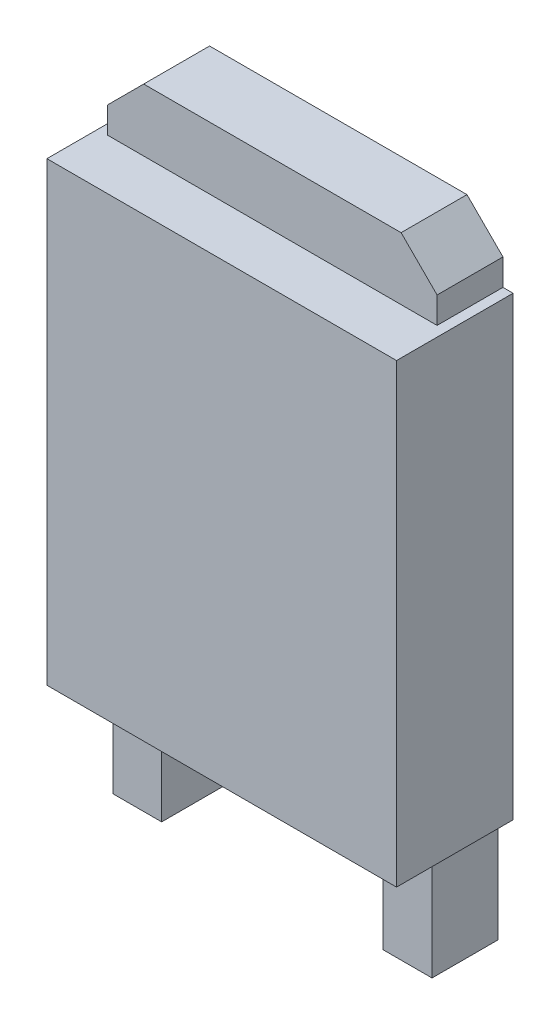
SolidWorks part; units mm, degrees
ref_plane "Front Plane" through (0, 0, 0) normal (0, 0, 1) x (1, 0, 0)
ref_plane "Top Plane" through (0, 0, 0) normal (0, 1, 0) x (1, 0, 0)
ref_plane "Right Plane" through (0, 0, 0) normal (1, 0, 0) x (0, 0, -1)
sketch "Sketch1" plane through (0, 0, 0) normal (0, 0, 1) x (1, 0, 0)
  line L1 (-3.45, -4.5) -> (3.45, -4.5)
  line L2 (-3.45, -4.5) -> (-3.45, 4.5)
  line L3 (-3.45, 4.5) -> (3.45, 4.5)
  line L4 (3.45, -4.5) -> (3.45, 4.5)
  line L5 (-3.45, -4.5) -> (3.45, 4.5) construction
  line L6 (-3.45, 4.5) -> (3.45, -4.5) construction
  point P0 (0, 0)
  dimension "D1" = 6.9
  dimension "D2" = 9
extrude "Boss-Extrude1" add sketch "Sketch1" along normal blind 2.3
sketch "Sketch2" plane through (0, 0, 0) normal (0, 0, -1) x (-1, 0, 0)
  line L0 (3.25, 4.5) -> (3.25, 5.0204)
  line L1 (-3.45, 4.5) -> (3.45, 4.5) construction
  line L2 (2.54, 5.7304) -> (-2.54, 5.7304)
  line L3 (-3.25, 5.0204) -> (-3.25, 4.5)
  line L4 (-3.25, 4.5) -> (3.25, 4.5)
  line L5 (-2.54, 5.7304) -> (-3.25, 5.0204)
  line L6 (3.25, 5.0204) -> (2.54, 5.7304)
  line L7 (-3.15, -4.5) -> (-3.15, -6.7031)
  line L8 (3.45, -4.5) -> (-3.45, -4.5) construction
  line L9 (-3.15, -6.7031) -> (-2.1853, -6.7031)
  line L10 (-2.1853, -6.7031) -> (-2.1853, -4.5)
  line L11 (-3.15, -4.5) -> (-2.1853, -4.5)
  line L12 (0, 0) -> (0, -2.7944) construction
  line L13 (3.15, -4.5) -> (3.15, -6.7031)
  line L14 (3.15, -6.7031) -> (2.1853, -6.7031)
  line L15 (2.1853, -6.7031) -> (2.1853, -4.5)
  line L16 (3.15, -4.5) -> (2.1853, -4.5)
  point P1 (3.25, 5.7304)
  point P5 (-3.25, 5.7304)
  dimension "D1" = 6.5
  dimension "D2" = 0.2
  dimension "D3" = 0.3
extrude "Boss-Extrude2" add sketch "Sketch2" against normal blind 1.3
sketch "Sketch3" plane through (0, 0, 0) normal (0, 0, -1) x (-1, 0, 0)
  line L0 (-3.25, 4.5) -> (-3.25, 5.0204)
  line L1 (-3.25, 5.0204) -> (-2.54, 5.7304)
  line L2 (-2.54, 5.7304) -> (2.54, 5.7304)
  line L3 (2.54, 5.7304) -> (3.25, 5.0204)
  line L4 (3.25, 5.0204) -> (3.25, 4.5)
  line L5 (3.25, 4.5) -> (-3.25, 4.5)
  line L6 (-3.15, -4.5) -> (-2.1853, -4.5)
  line L7 (-2.1853, -4.5) -> (-2.1853, -6.7031)
  line L8 (-2.1853, -6.7031) -> (-3.15, -6.7031)
  line L9 (-3.15, -6.7031) -> (-3.15, -4.5)
  line L10 (2.1853, -4.5) -> (3.15, -4.5)
  line L11 (3.15, -4.5) -> (3.15, -6.7031)
  line L12 (3.15, -6.7031) -> (2.1853, -6.7031)
  line L13 (2.1853, -6.7031) -> (2.1853, -4.5)
extrude "Boss-Extrude3" add sketch "Sketch3" along normal blind 0.0001
